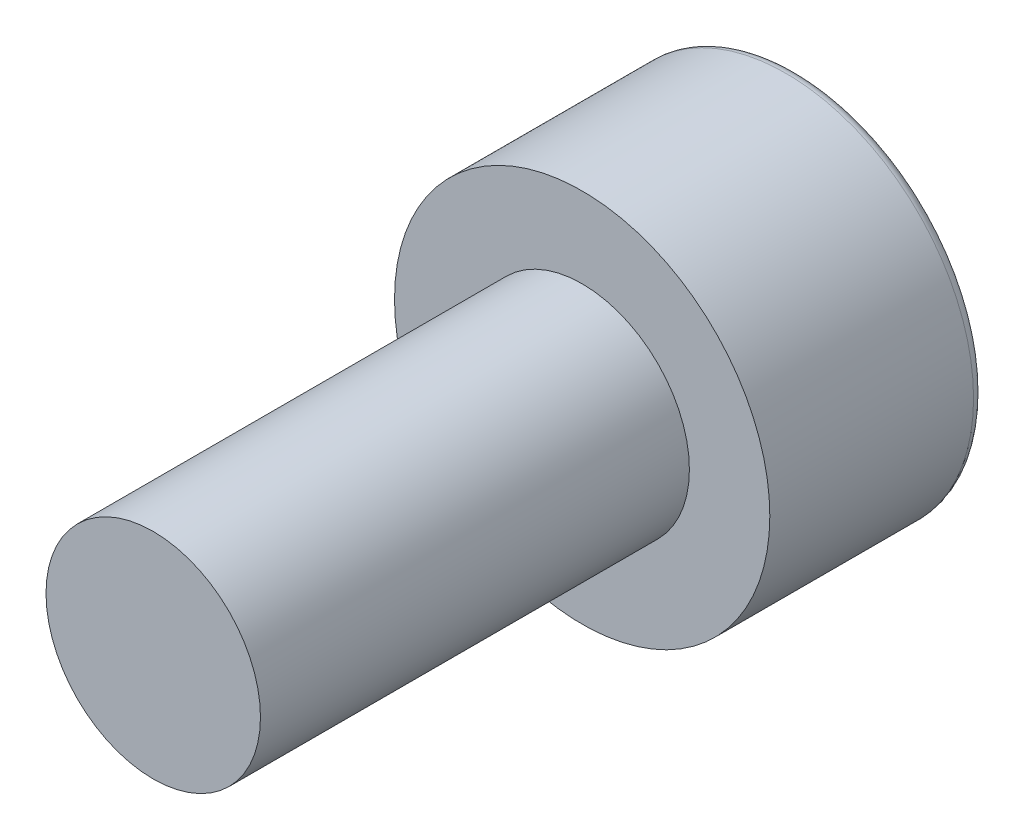
SolidWorks part; units mm, degrees
material "45"
ref_plane "前视基准面" through (0, 0, 0) normal (0, 0, 1) x (1, 0, 0)
ref_plane "上视基准面" through (0, 0, 0) normal (0, 1, 0) x (1, 0, 0)
ref_plane "右视基准面" through (0, 0, 0) normal (1, 0, 0) x (0, 0, -1)
sketch "草图1" plane through (0, 0, 0) normal (0, 0, 1) x (1, 0, 0)
  circle A0 centre (0, 0) radius 2
  dimension "D1" = 4
extrude "凸台-拉伸1" add sketch "草图1" along normal blind 8
cosmetic thread "装饰螺纹线1" parameters "D2"=3.242
sketch "草图2" plane through (0, 0, 0) normal (0, 0, 1) x (1, 0, 0)
  circle A0 centre (0, 0) radius 3.5
  dimension "D1" = 7
extrude "凸台-拉伸2" add sketch "草图2" against normal blind 4
sketch "草图3" plane through (0, 0, -4) normal (0, 0, -1) x (-1, 0, 0)
  line L0 (0, 5.5201) -> (0, -3.5199) construction
  line L1 (-3.9304, 0) -> (5.1097, 0) construction
  line L2 (0, 1.72) -> (-1.5, 0.8636)
  line L3 (-1.5, 0.8636) -> (-1.5, -0.8636)
  line L4 (-1.5, -0.8636) -> (0, -1.72)
  line L5 (0, -1.72) -> (1.5, -0.8636)
  line L6 (1.5, -0.8636) -> (1.5, 0.8636)
  line L7 (1.5, 0.8636) -> (0, 1.72)
  dimension "D1" = 3
  dimension "D2" = 3.44
extrude "切除-拉伸1" cut sketch "草图3" against normal blind 2
fillet "圆角1" radius 0.2 1 edges at (3.5, 0, -4)
equation "\"l\"=6"
equation "\"M\"=4"
equation "\"dk\"= 8.5"
equation "\"e\"= 4.58"
equation "\"k\"= 5"
equation "\"s\"= 4"
equation "\"t\"= 2.5"
equation "\"D1@草图1\"=\"M\""
equation "\"D1@凸台-拉伸1\"=\"l\""
equation "\"D1@草图2\"=\"dk\""
equation "\"D1@凸台-拉伸2\"=\"k\""
equation "\"D1@草图3\"=\"s\""
equation "\"D2@草图3\"=\"e\""
equation "\"D1@切除-拉伸1\"=\"t\""
